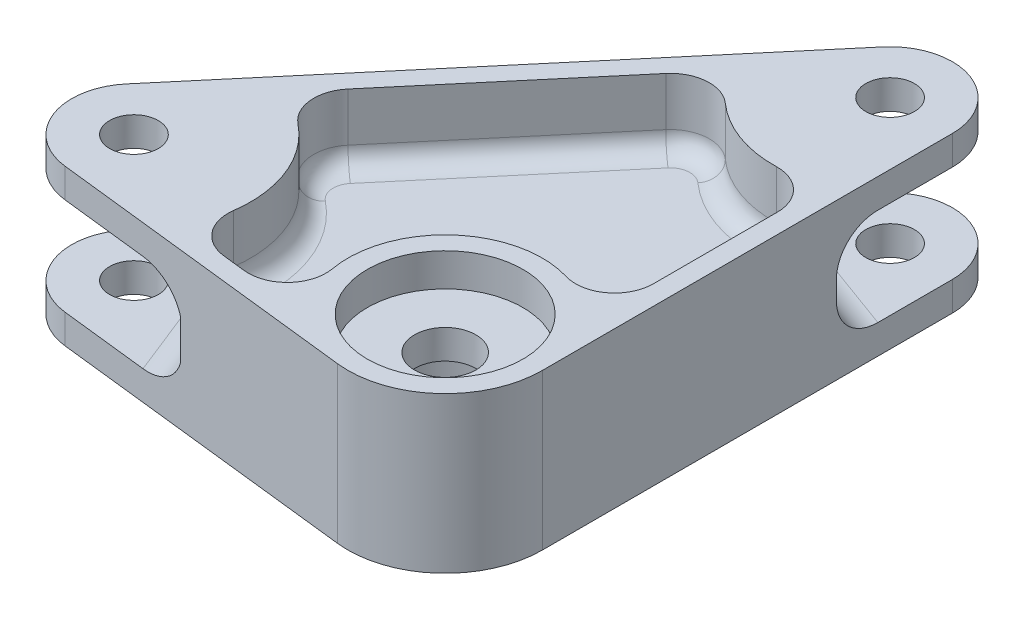
SolidWorks part; units mm, degrees
material "6061 Alloy"
ref_plane "Front Plane" through (0, 0, 0) normal (0, 0, 1) x (1, 0, 0)
ref_plane "Top Plane" through (0, 0, 0) normal (0, 1, 0) x (1, 0, 0)
ref_plane "Right Plane" through (0, 0, 0) normal (1, 0, 0) x (0, 0, -1)
sketch "Layout" plane through (0, 0, 0) normal (0, 1, 0) x (1, 0, 0)
  line L0 (0, 0) -> (-50.8, 0) construction
  line L1 (0, 0) -> (5.6801, 66.9424) construction
  dimension "D1" = 50.8
  dimension "D2" = 67.183
  dimension "D3" = 94.85
sketch "Sketch2" plane through (0, 0, 0) normal (0, 1, 0) x (1, 0, 0)
  line L0 (-58.5653, 6.5517) -> (-2.0852, 73.4942)
  line L1 (-51.943, -10.0955) -> (-1.7859, -15.7742)
  line L2 (15.875, 0.0083) -> (15.8401, 66.9477)
  arc A0 (-1.7859, -15.7742) -> (15.875, 0.0083) centre (0, 0) ccw
  arc A1 (-58.5653, 6.5517) -> (-51.943, -10.0955) centre (-50.8, 0) ccw
  arc A2 (15.8401, 66.9477) -> (-2.0852, 73.4942) centre (5.6801, 66.9424) ccw
  dimension "D1" = 15.875
  dimension "D2" = 10.16
  dimension "D3" = 10.16
extrude "Boss-Extrude2" add sketch "Sketch2" along normal mid plane 25.4
sketch "Sketch3" plane through (0, -12.7, 0) normal (0, -1, 0) x (1, 0, 0)
  circle A0 centre (0, 0) radius 12
  dimension "D1" = 24
extrude "Cut-Extrude1" cut sketch "Sketch3" against normal blind 15.24
sketch "Sketch5" plane through (0, 12.7, 0) normal (0, 1, 0) x (1, 0, 0)
  circle A0 centre (-50.8, 0) radius 3.9687
  circle A1 centre (5.6801, 66.9424) radius 3.9687
  dimension "D1" = 7.9375
extrude "Cut-Extrude3" cut sketch "Sketch5" against normal through all
sketch "Sketch4" plane through (0, 12.7, 0) normal (0, 1, 0) x (1, 0, 0)
  circle A0 centre (0, 0) radius 5
  dimension "D1" = 10
extrude "Cut-Extrude2" cut sketch "Sketch4" against normal through all
sketch "Sketch6" plane through (0, 12.7, 0) normal (0, 1, 0) x (1, 0, 0)
  line L1 (-39.7645, 23.9116) -> (-16.0327, 52.0395)
  line L2 (12.6889, 21.3052) -> (12.6784, 41.554)
  line L6 (-26.3549, -9.7973) -> (-22.5921, -10.2233)
  line L7 (-51.943, -10.0955) -> (-1.7859, -15.7742) construction
  line L8 (-58.5653, 6.5517) -> (-2.0852, 73.4942) construction
  line L9 (15.875, 0.0083) -> (15.8401, 66.9477) construction
  arc A0 (4.5278, 15.2156) -> (-15.6269, -2.7954) centre (0, 0) ccw
  arc A1 (-31.9304, -2.6157) -> (-38.8834, 14.8626) centre (-50.8, 0) ccw
  arc A2 (-6.9645, 52.6941) -> (6.1663, 47.8987) centre (5.6801, 66.9424) ccw
  arc A3 (-31.9304, -2.6157) -> (-26.3549, -9.7973) centre (-25.6406, -3.4876) ccw
  arc A4 (-38.8834, 14.8626) -> (-39.7645, 23.9116) centre (-34.9112, 19.8168) cw
  arc A5 (6.1663, 47.8987) -> (12.6784, 41.554) centre (6.3284, 41.5507) cw
  arc A6 (-6.9645, 52.6941) -> (-16.0327, 52.0395) centre (-11.1794, 47.9446) ccw
  arc A7 (12.6889, 21.3052) -> (4.5278, 15.2156) centre (6.3389, 21.3019) cw
  arc A8 (-15.6269, -2.7954) -> (-22.5921, -10.2233) centre (-21.8777, -3.9136) cw
  point P29 (12.8177, 0)
  dimension "D1" = 6.35
  dimension "D2" = 38.1
  dimension "D3" = 3.175
  dimension "D4" = 3.175
  dimension "D5" = 6.35
  dimension "D6" = 6.35
  dimension "D7" = 15.875
  dimension "D8" = 3.175
extrude "Cut-Extrude4" cut sketch "Sketch6" against normal blind 11.1125
sketch "Sketch8" plane through (0, -12.7, 0) normal (0, -1, 0) x (1, 0, 0)
  line L0 (-26.3549, 9.7973) -> (-22.5921, 10.2233)
  line L1 (-51.943, 10.0955) -> (-1.7859, 15.7742) construction
  line L2 (-39.7645, -23.9116) -> (-16.0327, -52.0395)
  line L4 (12.6784, -41.554) -> (12.6889, -21.3052)
  line L5 (15.875, -0.0083) -> (15.8401, -66.9477) construction
  line L6 (-58.5653, -6.5517) -> (-2.0852, -73.4942) construction
  arc A0 (-15.6269, 2.7954) -> (4.5278, -15.2156) centre (0, 0) ccw
  arc A1 (-38.8834, -14.8626) -> (-31.9304, 2.6157) centre (-50.8, 0) ccw
  arc A2 (6.1663, -47.8987) -> (-6.9645, -52.6941) centre (5.6801, -66.9424) ccw
  arc A3 (-22.5921, 10.2233) -> (-15.6269, 2.7954) centre (-21.8777, 3.9136) cw
  arc A4 (12.6889, -21.3052) -> (4.5278, -15.2156) centre (6.3389, -21.3019) ccw
  arc A5 (12.6784, -41.554) -> (6.1663, -47.8987) centre (6.3284, -41.5507) cw
  arc A6 (-6.9645, -52.6941) -> (-16.0327, -52.0395) centre (-11.1794, -47.9446) cw
  arc A7 (-39.7645, -23.9116) -> (-38.8834, -14.8626) centre (-34.9112, -19.8168) cw
  arc A8 (-31.9304, 2.6157) -> (-26.3549, 9.7973) centre (-25.6406, 3.4876) cw
  point P22 (-50.8, 9.525)
  dimension "D1" = 31.75
  dimension "D2" = 38.1
  dimension "D3" = 3.175
  dimension "D4" = 3.175
  dimension "D5" = 3.175
  dimension "D6" = 6.35
extrude "Cut-Extrude5" cut sketch "Sketch8" against normal blind 11.1125
sketch "Sketch10" plane through (0, 12.7, 0) normal (0, 1, 0) x (1, 0, 0)
  circle A0 centre (0, 0) radius 12.7
  dimension "D1" = 25.4
extrude "Cut-Extrude6" cut sketch "Sketch10" against normal blind 5.3975
sketch "Sketch11" plane through (0, 12.7, 0) normal (0, 1, 0) x (1, 0, 0)
  line L0 (-14.2922, 59.026) -> (15.85, 48.0179) construction
  line L1 (-58.5653, 6.5517) -> (-2.0852, 73.4942) construction
  line L2 (15.875, 0.0083) -> (15.8401, 66.9477) construction
  line L3 (-44.6098, 23.0924) -> (-30.4389, -12.5302) construction
  line L4 (-51.943, -10.0955) -> (-1.7859, -15.7742) construction
  line L5 (-58.5653, 6.5517) -> (-44.6098, 23.0924) construction
  line L6 (-51.943, -10.0955) -> (-30.4389, -12.5302) construction
  line L7 (-2.0852, 73.4942) -> (-14.2922, 59.026) construction
  line L8 (15.8401, 66.9477) -> (15.85, 48.0179) construction
  circle A0 centre (-50.8, 0) radius 14.2875 construction
  circle A1 centre (5.6801, 66.9424) radius 14.2875 construction
  dimension "D1" = 28.575
ref_plane "Plane1" through (-30.5837, 0, 12.1663) normal (-0.9292, 0, 0.3696) x (0.3696, 0, 0.9292)
ref_plane "Plane2" through (17.3379, 0, -47.4745) normal (-0.343, 0, 0.9393) x (0.9393, 0, 0.343)
sketch "Sketch12" plane through (17.3379, 0, -47.4745) normal (-0.343, 0, 0.9393) x (0.9393, 0, 0.343)
  line L0 (-17.6287, 9.3704) -> (-17.6287, -11.0985) construction
  line L1 (1.4213, 7.9375) -> (-36.6787, 7.9375)
  line L2 (1.4213, 7.9375) -> (1.4213, -7.9375)
  line L3 (1.4213, -7.9375) -> (-36.6787, -7.9375)
  line L4 (-33.6734, 12.7) -> (-1.584, 12.7) construction
  line L5 (-33.6734, 12.7) -> (-1.584, 12.7) construction
  line L6 (-27.1704, -12.7) -> (-8.0871, -12.7) construction
  line L7 (-27.1704, -12.7) -> (-8.0871, -12.7) construction
  line L8 (-36.6787, 7.9375) -> (-36.6787, -7.9375)
  point P6 (-17.6287, -7.9375)
  dimension "D1" = 4.7625
  dimension "D2" = 4.7625
  dimension "D3" = 15.875
  dimension "D4" = 38.1
extrude "Cut-Extrude7" cut sketch "Sketch12" against normal up to next
sketch "Sketch15" plane through (-30.5837, 0, 12.1663) normal (-0.9292, 0, 0.3696) x (0.3696, 0, 0.9292)
  line L0 (-18.7773, 9.5144) -> (-18.7773, -9.5144) construction
  line L1 (0, 0) -> (-60.1019, 0) construction
  line L3 (-27.7353, -12.7) -> (-9.8193, -12.7) construction
  line L4 (-27.7353, -12.7) -> (-9.8193, -12.7) construction
  line L6 (-37.8273, 7.9375) -> (0.2727, 7.9375)
  line L7 (0.2727, 7.9375) -> (0.2727, -7.9375)
  line L8 (0.2727, -7.9375) -> (-37.8273, -7.9375)
  line L9 (-37.8273, -7.9375) -> (-37.8273, 7.9375)
  point P2 (-37.8273, 0)
  point P7 (-18.7773, 0)
  point P13 (-18.7773, 7.9375)
  dimension "D1" = 15.875
  dimension "D2" = 38.1
extrude "Cut-Extrude8" cut sketch "Sketch15" along normal up to next
fillet "Fillet1" radius 3.175 12 edges at (-10.5781, 1.5875, -11.8372) (-17.2456, 1.5875, 8.2571) (-24.4735, 1.5875, 10.0103) (-30.6564, 1.5875, 7.3817) (-33.0992, 1.5875, -7.0415) (-41.2313, 1.5875, -19.2014) (-27.8986, 1.5875, -37.9755) (-11.6366, 1.5875, -54.2781) (-0.8548, 1.5875, -49.0484) (10.7596, 1.5875, -46.0989) (12.6836, 1.5875, -31.4296) (10.1364, 1.5875, -16.2125)
fillet "Fillet2" radius 3.175 12 edges at (-41.2313, -1.5875, -19.2014) (-33.0992, -1.5875, -7.0415) (-30.6564, -1.5875, 7.3817) (-24.4735, -1.5875, 10.0103) (-17.2456, -1.5875, 8.2571) (-10.5781, -1.5875, -11.8372) (10.1364, -1.5875, -16.2125) (12.6836, -1.5875, -31.4296) (10.7596, -1.5875, -46.0989) (-0.8548, -1.5875, -49.0484) (-11.6366, -1.5875, -54.2781) (-27.8986, -1.5875, -37.9755)
fillet "Fillet3" radius 6.35 4 edges at (0.7789, 7.9375, -53.5219) (0.7789, -7.9375, -53.5219) (-37.5244, 7.9375, -5.2811) (-37.5244, -7.9375, -5.2811)
chamfer "Chamfer1" distance 0.635 angle 45 1 edges at (0, -12.7, -12)
